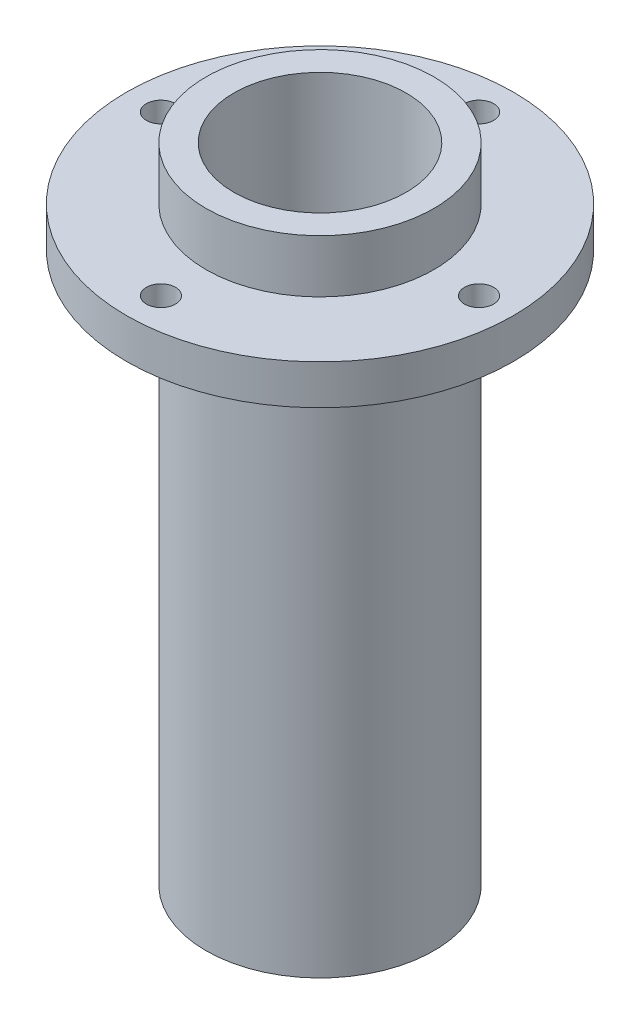
SolidWorks part; units mm, degrees
ref_plane "Front Plane" through (0, 0, 0) normal (0, 0, 1) x (1, 0, 0)
ref_plane "Top Plane" through (0, 0, 0) normal (0, 1, 0) x (1, 0, 0)
ref_plane "Right Plane" through (0, 0, 0) normal (1, 0, 0) x (0, 0, -1)
sketch "Sketch1" plane through (0, 0, 0) normal (0, 0, 1) x (1, 0, 0)
  line L1 (-8.6, 20.75) -> (0, 20.75)
  line L2 (-8.6, 20.75) -> (-8.6, 16.75)
  line L6 (-8.6, 13.75) -> (-8.6, -27.75)
  line L7 (-14.6, 16.75) -> (-8.6, 16.75)
  line L8 (-14.6, 16.75) -> (-14.6, 13.75)
  line L9 (-14.6, 13.75) -> (-8.6, 13.75)
  line L10 (0, 20.75) -> (0, -20.75)
  line L13 (0, -20.75) -> (-6.6, -20.75)
  line L14 (-6.6, -20.75) -> (-6.6, -27.75)
  line L15 (-6.6, -27.75) -> (-8.6, -27.75)
  point P3 (0, 0)
  dimension "D1" = 37.5
  dimension "D2" = 6.6
  dimension "D3" = 2
  dimension "D4" = 7
  dimension "D5" = 3
  dimension "D6" = 4
  dimension "D7" = 6
revolve "Revolve1" add sketch "Sketch1" angle 360 about L10
chamfer "Chamfer1" distance 0.5 angle 45 1 edges at (0, -27.75, 6.6)
sketch "Sketch2" plane through (0, 16.75, 0) normal (0, 1, 0) x (1, 0, 0)
  circle A0 centre (0, 12) radius 1.1
  circle A1 centre (12, 0) radius 1.1
  circle A2 centre (0, -12) radius 1.1
  circle A3 centre (-12, 0) radius 1.1
  circle A4 centre (0, 0) radius 8.6 construction
  point P10 (0, 0)
  dimension "D1" = 2.2
  dimension "D3" = 12
  dimension "D2" = 4
extrude "Cut-Extrude1" cut sketch "Sketch2" against normal up to next
sketch "Sketch3" plane through (0, 20.75, 0) normal (0, 1, 0) x (1, 0, 0)
  circle A0 centre (0, 0) radius 6.5
  dimension "D1" = 13
extrude "Cut-Extrude2" cut sketch "Sketch3" against normal blind 38
